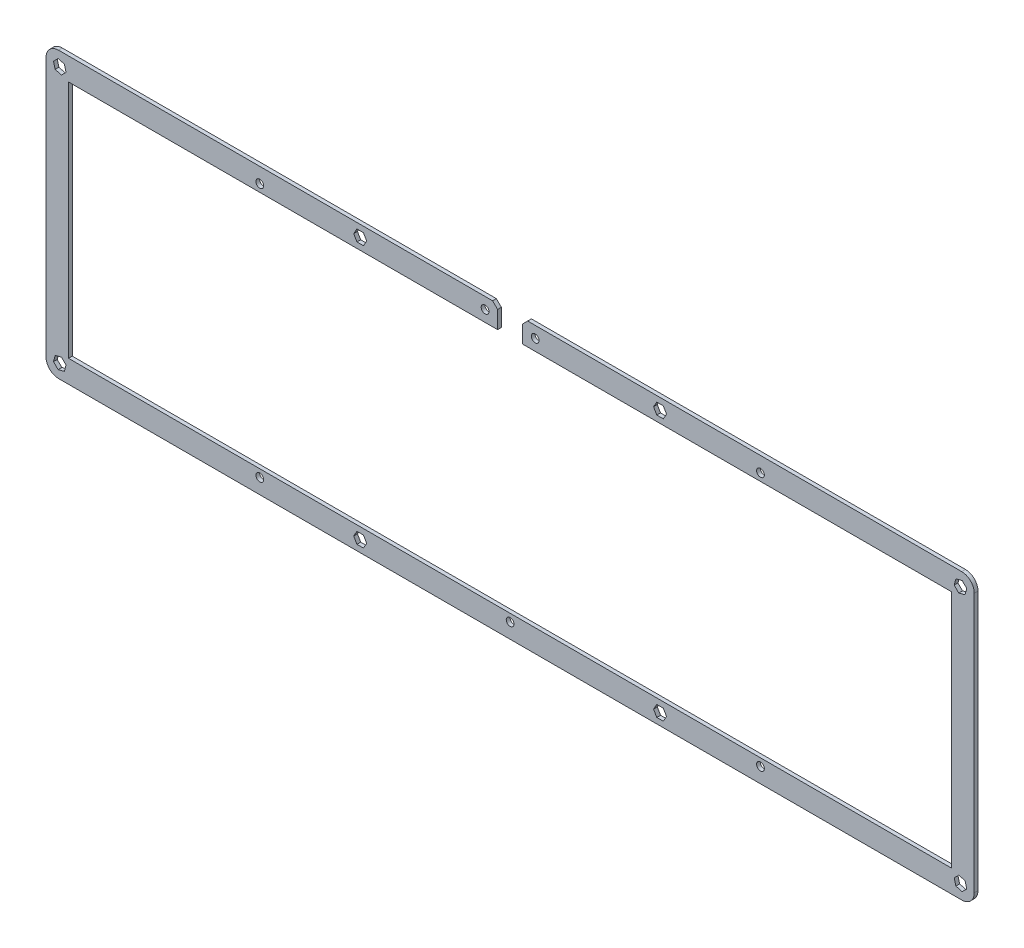
SolidWorks part; units mm, degrees
ref_plane "Front Plane" through (0, 0, 0) normal (0, 0, 1) x (1, 0, 0)
ref_plane "Top Plane" through (0, 0, 0) normal (0, 1, 0) x (1, 0, 0)
ref_plane "Right Plane" through (0, 0, 0) normal (1, 0, 0) x (0, 0, -1)
sketch "Model" plane through (0, 0, 0) normal (0, 0, 1) x (1, 0, 0)
  line L0 (0, 108.6) -> (0, 5)
  line L1 (9, 104.6) -> (9, 9)
  line L2 (365.775, 0) -> (5, 0)
  line L3 (361.775, 9) -> (9, 9)
  line L4 (370.775, 108.6) -> (370.775, 5)
  line L5 (361.775, 104.6) -> (361.775, 9)
  line L6 (180.3875, 104.6) -> (180.3875, 111.6)
  line L7 (180.3875, 111.6) -> (178.3875, 113.6)
  line L8 (190.3875, 111.6) -> (192.3875, 113.6)
  line L9 (190.3875, 104.6) -> (190.3875, 111.6)
  line L10 (9, 104.6) -> (180.3875, 104.6)
  line L11 (5, 113.6) -> (178.3875, 113.6)
  line L12 (190.3875, 104.6) -> (361.775, 104.6)
  line L13 (192.3875, 113.6) -> (365.775, 113.6)
  line L14 (365.9474, 110.6095) -> (367.7845, 108.7724)
  line L15 (367.7845, 108.7724) -> (367.1121, 106.2629)
  line L16 (367.1121, 106.2629) -> (364.6026, 105.5905)
  line L17 (364.6026, 105.5905) -> (362.7655, 107.4276)
  line L18 (362.7655, 107.4276) -> (363.4379, 109.9371)
  line L19 (363.4379, 109.9371) -> (365.9474, 110.6095)
  line L20 (4.8276, 110.6095) -> (2.9905, 108.7724)
  line L21 (2.9905, 108.7724) -> (3.6629, 106.2629)
  line L22 (3.6629, 106.2629) -> (6.1724, 105.5905)
  line L23 (6.1724, 105.5905) -> (8.0095, 107.4276)
  line L24 (8.0095, 107.4276) -> (7.3371, 109.9371)
  line L25 (7.3371, 109.9371) -> (4.8276, 110.6095)
  line L26 (365.9474, 2.9905) -> (367.7845, 4.8276)
  line L27 (367.7845, 4.8276) -> (367.1121, 7.3371)
  line L28 (367.1121, 7.3371) -> (364.6026, 8.0095)
  line L29 (364.6026, 8.0095) -> (362.7655, 6.1724)
  line L30 (362.7655, 6.1724) -> (363.4379, 3.6629)
  line L31 (363.4379, 3.6629) -> (365.9474, 2.9905)
  line L32 (4.8276, 2.9905) -> (2.9905, 4.8276)
  line L33 (2.9905, 4.8276) -> (3.6629, 7.3371)
  line L34 (3.6629, 7.3371) -> (6.1724, 8.0095)
  line L35 (6.1724, 8.0095) -> (8.0095, 6.1724)
  line L36 (8.0095, 6.1724) -> (7.3371, 3.6629)
  line L37 (7.3371, 3.6629) -> (4.8276, 2.9905)
  line L38 (243.976, 2.25) -> (246.574, 2.25)
  line L39 (246.574, 2.25) -> (247.8731, 4.5)
  line L40 (247.8731, 4.5) -> (246.574, 6.75)
  line L41 (246.574, 6.75) -> (243.976, 6.75)
  line L42 (243.976, 6.75) -> (242.6769, 4.5)
  line L43 (242.6769, 4.5) -> (243.976, 2.25)
  line L44 (243.976, 106.85) -> (246.574, 106.85)
  line L45 (246.574, 106.85) -> (247.8731, 109.1)
  line L46 (247.8731, 109.1) -> (246.574, 111.35)
  line L47 (246.574, 111.35) -> (243.976, 111.35)
  line L48 (243.976, 111.35) -> (242.6769, 109.1)
  line L49 (242.6769, 109.1) -> (243.976, 106.85)
  line L50 (124.201, 106.85) -> (126.799, 106.85)
  line L51 (126.799, 106.85) -> (128.0981, 109.1)
  line L52 (128.0981, 109.1) -> (126.799, 111.35)
  line L53 (126.799, 111.35) -> (124.201, 111.35)
  line L54 (124.201, 111.35) -> (122.9019, 109.1)
  line L55 (122.9019, 109.1) -> (124.201, 106.85)
  line L56 (124.201, 2.25) -> (126.799, 2.25)
  line L57 (126.799, 2.25) -> (128.0981, 4.5)
  line L58 (128.0981, 4.5) -> (126.799, 6.75)
  line L59 (126.799, 6.75) -> (124.201, 6.75)
  line L60 (124.201, 6.75) -> (122.9019, 4.5)
  line L61 (122.9019, 4.5) -> (124.201, 2.25)
  arc A0 (365.775, 0) -> (370.775, 5) centre (365.775, 5) ccw
  arc A1 (370.775, 108.6) -> (365.775, 113.6) centre (365.775, 108.6) ccw
  arc A2 (0, 5) -> (5, 0) centre (5, 5) ccw
  arc A3 (5, 113.6) -> (0, 108.6) centre (5, 108.6) ccw
  circle A4 centre (195.3875, 109.1) radius 1.55
  circle A5 centre (175.3875, 109.1) radius 1.55
  circle A6 centre (85.3875, 107.6) radius 1.55
  circle A7 centre (285.3875, 107.6) radius 1.55
  circle A8 centre (85.3875, 6) radius 1.55
  circle A9 centre (185.3875, 6) radius 1.55
  circle A10 centre (285.3875, 6) radius 1.55
  dimension "D1" = 3.1
  dimension "D2" = 3.1
extrude "Boss-Extrude1" add sketch "Model" along normal blind 1.5
